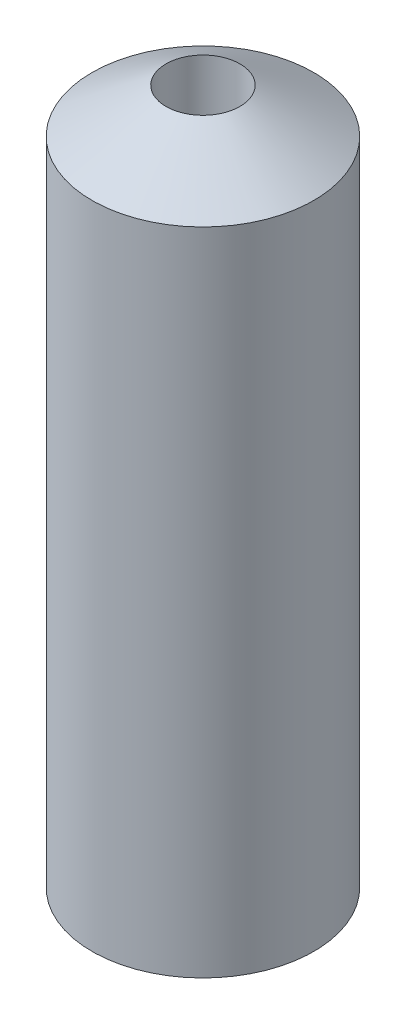
SolidWorks part; units mm, degrees
ref_plane "Front Plane" through (0, 0, 0) normal (0, 0, 1) x (1, 0, 0)
ref_plane "Top Plane" through (0, 0, 0) normal (0, 1, 0) x (1, 0, 0)
ref_plane "Right Plane" through (0, 0, 0) normal (1, 0, 0) x (0, 0, -1)
sketch "Sketch1" plane through (0, 0, 0) normal (0, 0, 1) x (1, 0, 0)
  line L0 (0, 13.2987) -> (0, -17.6873) construction
  line L1 (0.5, 10) -> (0.5, 0)
  line L2 (0.5, 0) -> (1.5, 0.6009)
  line L3 (1.5, 0.6009) -> (1.5, 9.3991)
  line L4 (1.5, 9.3991) -> (0.5, 10)
  point P5 (1.5, 10.7094)
  point P8 (0, 0)
  dimension "D1" = 59
  dimension "D2" = 1
  dimension "D3" = 3
  dimension "D4" = 10
revolve "Revolve1" add sketch "Sketch1" angle 360 about L0
